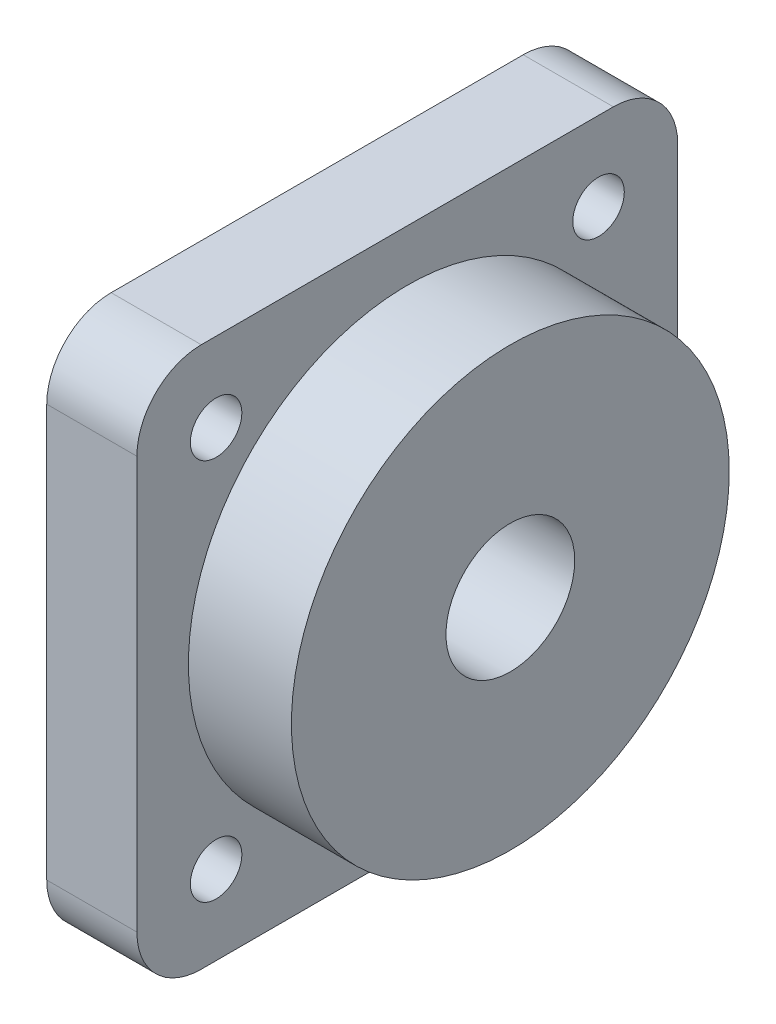
SolidWorks part; units mm, degrees
ref_plane "Front Plane" through (0, 0, 0) normal (0, 0, 1) x (1, 0, 0)
ref_plane "Top Plane" through (0, 0, 0) normal (0, 1, 0) x (1, 0, 0)
ref_plane "Right Plane" through (0, 0, 0) normal (1, 0, 0) x (0, 0, -1)
sketch "Sketch1" plane through (0, 0, 0) normal (1, 0, 0) x (0, 0, -1)
  line L1 (21, -21) -> (-21, -21)
  line L2 (21, -21) -> (21, 21)
  line L3 (21, 21) -> (-21, 21)
  line L4 (-21, -21) -> (-21, 21)
  line L5 (21, -21) -> (-21, 21) construction
  line L6 (21, 21) -> (-21, -21) construction
  circle A0 centre (-14.8492, 14.8492) radius 2
  circle A1 centre (14.8492, 14.8492) radius 2
  circle A2 centre (14.8492, -14.8492) radius 2
  circle A3 centre (-14.8492, -14.8492) radius 2
  circle A4 centre (0, 0) radius 10
  point P0 (0, 0)
  dimension "D2" = 4
  dimension "D4" = 20
  dimension "D1" = 42
  dimension "D3" = 42
extrude "Boss-Extrude1" add sketch "Sketch1" along normal blind 7
sketch "Sketch2" plane through (0, 0, 0) normal (1, 0, 0) x (0, 0, -1)
  circle A0 centre (0, 0) radius 17
  circle A1 centre (0, 0) radius 5
  dimension "D1" = 10
  dimension "D2" = 34
extrude "Boss-Extrude2" add sketch "Sketch2" along normal blind 15
fillet "Fillet1" radius 5 4 edges at (3.5, 21, 21) (3.5, 21, -21) (3.5, -21, -21) (3.5, -21, 21)
